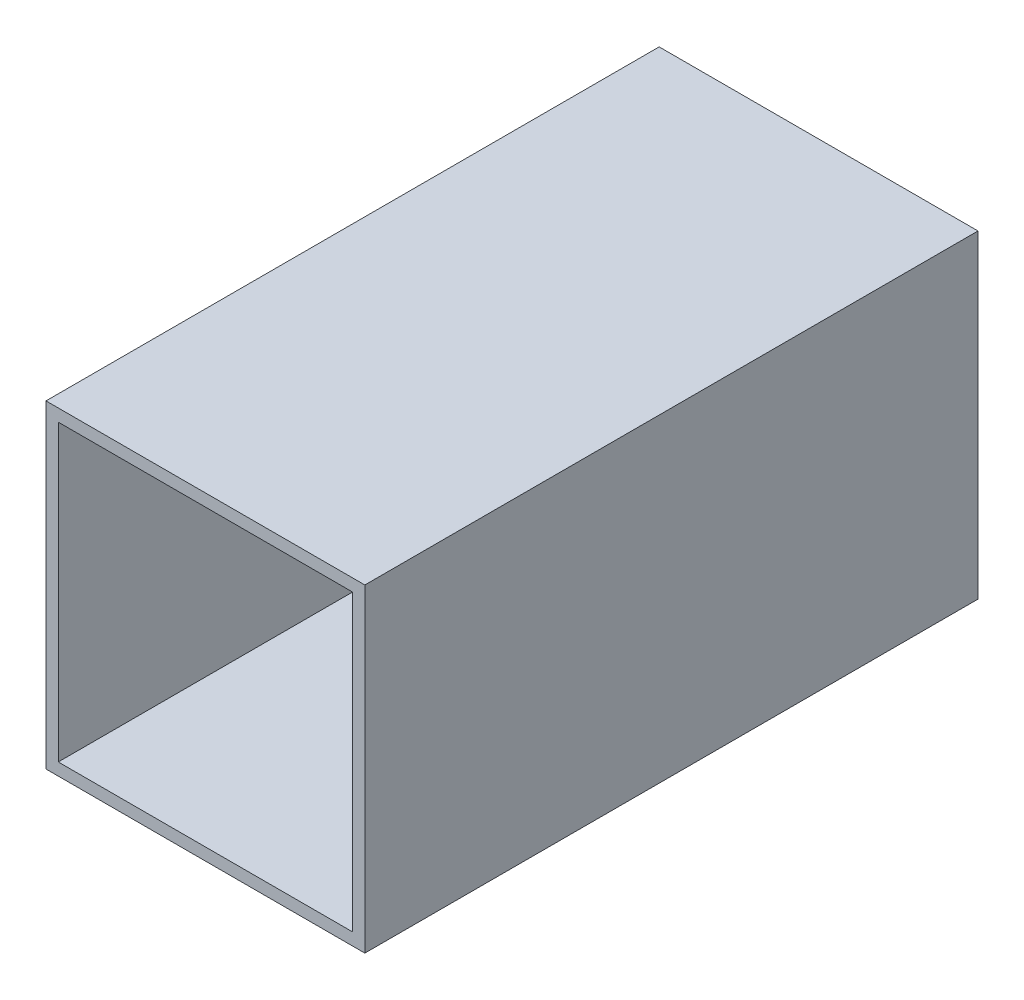
SolidWorks part; units mm, degrees
ref_plane "Front Plane" through (0, 0, 0) normal (0, 0, 1) x (1, 0, 0)
ref_plane "Top Plane" through (0, 0, 0) normal (0, 1, 0) x (1, 0, 0)
ref_plane "Right Plane" through (0, 0, 0) normal (1, 0, 0) x (0, 0, -1)
sketch "Sketch1" plane through (0, 0, 0) normal (0, 0, 1) x (1, 0, 0)
  line L5 (-36.576, 36.576) -> (36.576, 36.576)
  line L6 (-36.576, 36.576) -> (-36.576, -36.576)
  line L11 (-36.576, -36.576) -> (36.576, -36.576)
  line L12 (36.576, 36.576) -> (36.576, -36.576)
  line L13 (-36.576, 36.576) -> (36.576, -36.576) construction
  line L14 (-36.576, -36.576) -> (36.576, 36.576) construction
  line L15 (39.624, -39.624) -> (-39.624, -39.624)
  line L16 (39.624, -39.624) -> (39.624, 39.624)
  line L17 (39.624, 39.624) -> (-39.624, 39.624)
  line L18 (-39.624, -39.624) -> (-39.624, 39.624)
  line L19 (39.624, -39.624) -> (-39.624, 39.624) construction
  line L20 (39.624, 39.624) -> (-39.624, -39.624) construction
  point P0 (0, 0)
  point P6 (0, 0)
  dimension "D1" = 3.048
  dimension "D3" = 76.2
extrude "Boss-Extrude1" add sketch "Sketch1" along normal blind 152.4
